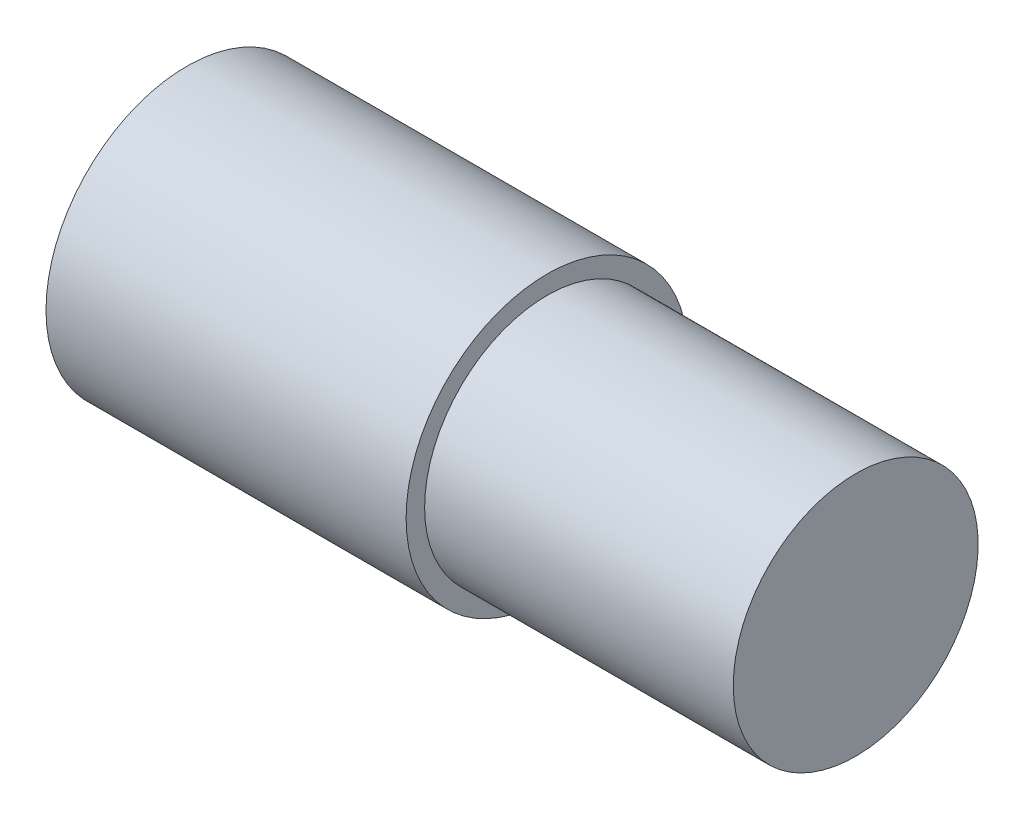
SolidWorks part; units mm, degrees
ref_plane "Front Plane" through (0, 0, 0) normal (0, 0, 1) x (1, 0, 0)
ref_plane "Top Plane" through (0, 0, 0) normal (0, 1, 0) x (1, 0, 0)
ref_plane "Right Plane" through (0, 0, 0) normal (1, 0, 0) x (0, 0, -1)
sketch "Sketch1" plane through (0, 0, 0) normal (0, 0, 1) x (1, 0, 0)
  line L0 (-28.9907, 0) -> (79.8237, 0) construction
  line L1 (0, 63.3427) -> (0, -69.6968) construction
  line L2 (44.45, 17.399) -> (44.45, 15.113)
  line L3 (0, 0) -> (82.55, 0)
  line L4 (0, 0) -> (0, 17.399)
  line L5 (0, 17.399) -> (44.45, 17.399)
  line L6 (44.45, 15.113) -> (82.55, 15.113)
  line L7 (82.55, 15.113) -> (82.55, 0)
  point P8 (46.924, 17.399)
  point P9 (72.4225, 0)
  dimension "D1" = 34.798
  dimension "D2" = 30.226
  dimension "D3" = 44.45
  dimension "D4" = 82.55
revolve "Revolve1" add sketch "Sketch1" angle 360 about L0
